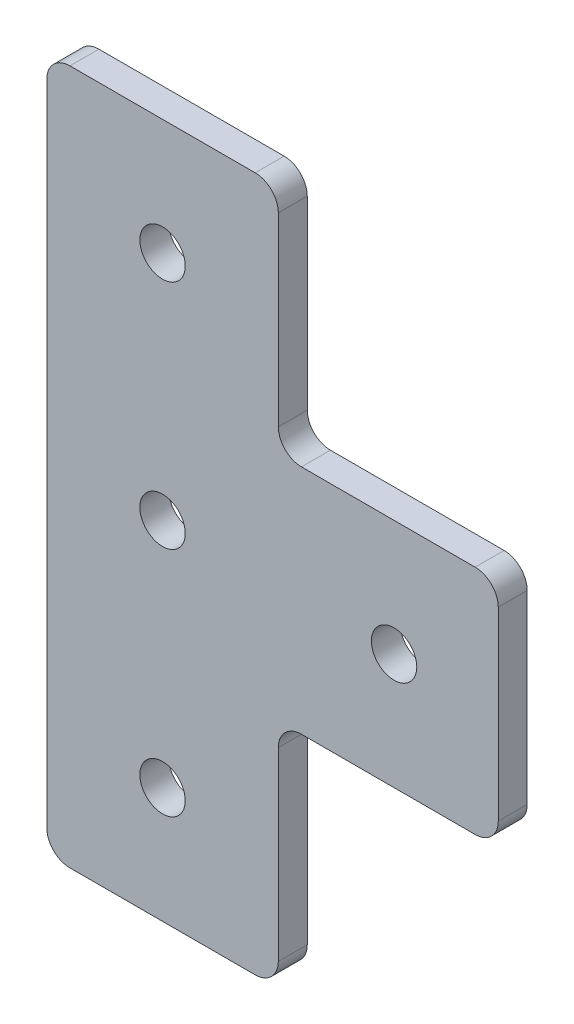
SolidWorks part; units mm, degrees
ref_plane "Front Plane" through (0, 0, 0) normal (0, 0, 1) x (1, 0, 0)
ref_plane "Top Plane" through (0, 0, 0) normal (0, 1, 0) x (1, 0, 0)
ref_plane "Right Plane" through (0, 0, 0) normal (1, 0, 0) x (0, 0, -1)
sketch "Sketch1" plane through (0, 0, 0) normal (0, 0, 1) x (1, 0, 0)
  line L0 (-2.54, 0) -> (-21.59, 0)
  line L1 (-24.13, -2.54) -> (-24.13, -22.86)
  line L2 (-26.67, -25.4) -> (-46.99, -25.4)
  line L3 (-49.53, -22.86) -> (-49.53, 48.26)
  line L4 (-46.99, 50.8) -> (-26.67, 50.8)
  line L5 (-24.13, 48.26) -> (-24.13, 27.94)
  line L6 (-21.59, 25.4) -> (-2.54, 25.4)
  line L7 (0, 22.86) -> (0, 2.54)
  circle A0 centre (-36.83, 38.1) radius 2.4892
  circle A1 centre (-36.83, 12.7) radius 2.4892
  circle A2 centre (-36.83, -12.7) radius 2.4892
  circle A3 centre (-11.43, 12.7) radius 2.4892
  arc A4 (-2.54, 0) -> (0, 2.54) centre (-2.54, 2.54) ccw
  arc A5 (-2.54, 25.4) -> (0, 22.86) centre (-2.54, 22.86) cw
  arc A6 (-24.13, 27.94) -> (-21.59, 25.4) centre (-21.59, 27.94) ccw
  arc A7 (-21.59, 0) -> (-24.13, -2.54) centre (-21.59, -2.54) ccw
  arc A8 (-24.13, -22.86) -> (-26.67, -25.4) centre (-26.67, -22.86) cw
  arc A9 (-46.99, -25.4) -> (-49.53, -22.86) centre (-46.99, -22.86) cw
  arc A10 (-26.67, 50.8) -> (-24.13, 48.26) centre (-26.67, 48.26) cw
  arc A11 (-49.53, 48.26) -> (-46.99, 50.8) centre (-46.99, 48.26) cw
  point P17 (0, 12.7)
  point P18 (0, 0)
  point P19 (0, 0)
  point P20 (0, 0)
  point P21 (0, 0)
  point P22 (-36.83, 50.8)
  point P25 (0, 0)
  point P28 (0, 25.4)
  point P31 (-24.13, 25.4)
  point P36 (-24.13, -25.4)
  point P39 (-49.53, -25.4)
  point P44 (-49.53, 50.8)
  dimension "D5" = 4.9784
  dimension "D6" = 25.4
  dimension "D7" = 25.4
  dimension "D8" = 25.4
  dimension "D9" = 2.54
  dimension "D1" = 25.4
  dimension "D2" = 25.4
  dimension "D3" = 76.2
  dimension "D4" = 24.13
extrude "Boss-Extrude1" add sketch "Sketch1" along normal blind 3.175
